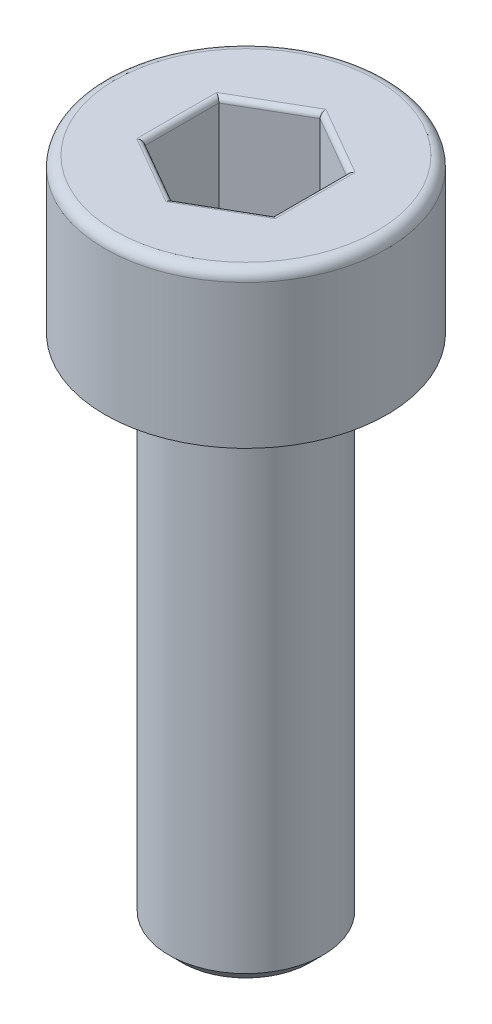
SolidWorks part; units mm, degrees
ref_plane "Front Plane" through (0, 0, 0) normal (0, 0, 1) x (1, 0, 0)
ref_plane "Top Plane" through (0, 0, 0) normal (0, 1, 0) x (1, 0, 0)
ref_plane "Right Plane" through (0, 0, 0) normal (1, 0, 0) x (0, 0, -1)
sketch "Sketch1" plane through (0, 0, 0) normal (0, 0, 1) x (1, 0, 0)
  line L0 (0, 0) -> (0, -47.0967) construction
  line L1 (0, -13) -> (-1.5, -13)
  line L2 (-1.5, -13) -> (-1.5, -3)
  line L3 (-1.5, -3) -> (-2.75, -3)
  line L4 (-2.75, -3) -> (-2.75, 0)
  line L5 (-2.75, 0) -> (0, 0)
  line L6 (0, 0) -> (0, -13)
  dimension "D1" = 10
  dimension "d" = 3
  dimension "k" = 3
  dimension "dk" = 5.5
revolve "Revolve1" add sketch "Sketch1" angle 360 about L0
chamfer "Chamfer1" distance 0.25 angle 45 2 edges at (0, -3, 1.5) (0, -13, 1.5)
fillet "Fillet1" radius 0.2 1 edges at (0, 0, 2.75)
sketch "Sketch2" plane through (0, 0, 0) normal (0, 1, 0) x (1, 0, 0)
  line L1 (0, 1.4434) -> (-1.25, 0.7217)
  line L2 (-1.25, 0.7217) -> (-1.25, -0.7217)
  line L3 (-1.25, -0.7217) -> (0, -1.4434)
  line L4 (0, -1.4434) -> (1.25, -0.7217)
  line L5 (1.25, -0.7217) -> (1.25, 0.7217)
  line L6 (1.25, 0.7217) -> (0, 1.4434)
  circle A0 centre (0, 0) radius 1.25 construction
  dimension "s" = 2.5
extrude "Cut-Extrude1" cut sketch "Sketch2" against normal blind 2
fillet "Fillet2" radius 0.1 12 edges at (-0.625, 0, -1.0825) (-1.25, 0, 0) (-0.625, 0, 1.0825) (0.625, 0, 1.0825) (1.25, 0, 0) (0.625, 0, -1.0825) (1.25, -2, 0) (0.625, -2, 1.0825) (-0.625, -2, 1.0825) (-1.25, -2, 0) (-0.625, -2, -1.0825) (0.625, -2, -1.0825)
